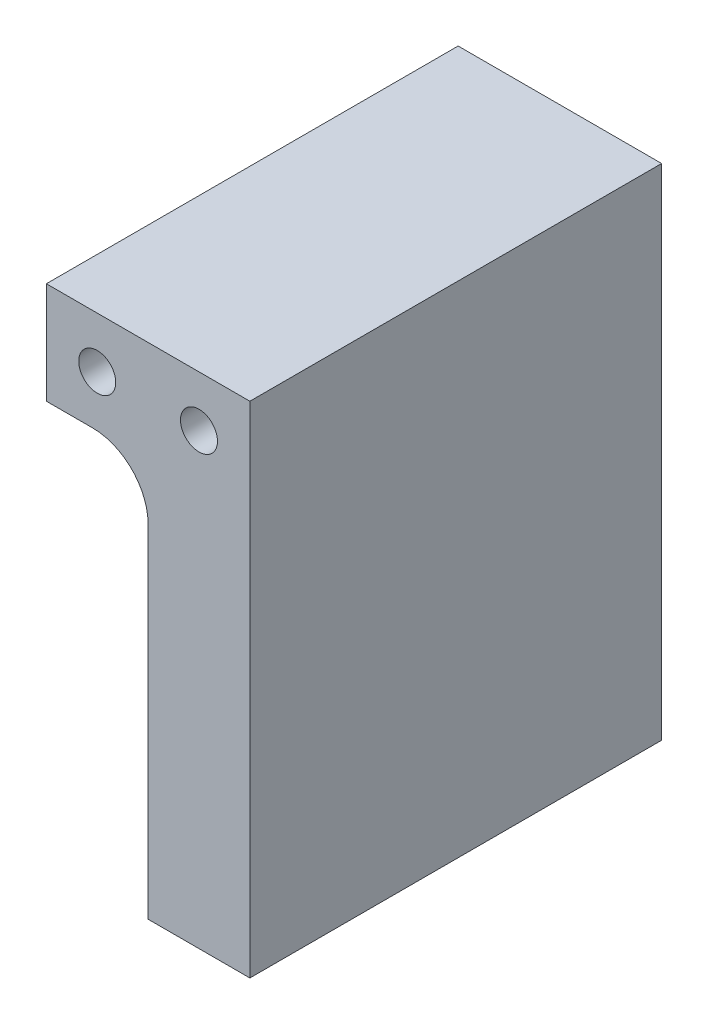
SolidWorks part; units mm, degrees
ref_plane "Front Plane" through (0, 0, 0) normal (0, 0, 1) x (1, 0, 0)
ref_plane "Top Plane" through (0, 0, 0) normal (0, 1, 0) x (1, 0, 0)
ref_plane "Right Plane" through (0, 0, 0) normal (1, 0, 0) x (0, 0, -1)
sketch "Sketch1" plane through (0, 0, 0) normal (0, 0, 1) x (1, 0, 0)
  line L0 (0, 0) -> (-110, 0)
  line L1 (-110, 0) -> (-110, -55)
  line L2 (-110, -55) -> (-85, -55)
  line L3 (-55, -85) -> (-55, -270)
  line L4 (-55, -270) -> (0, -270)
  line L5 (0, -270) -> (0, 0)
  arc A0 (-85, -55) -> (-55, -85) centre (-85, -85) cw
  dimension "D5" = 30
  dimension "D1" = 110
  dimension "D2" = 270
  dimension "D3" = 55
  dimension "D4" = 55
extrude "Boss-Extrude1" add sketch "Sketch1" along normal blind 222.57
sketch "Sketch2" plane through (0, 0, 222.57) normal (0, 0, 1) x (1, 0, 0)
  line L0 (-110, -55) -> (0, -55) construction
  line L1 (0, -270) -> (0, 0) construction
  line L2 (-55, -55) -> (-55, 0) construction
  line L3 (0, 0) -> (-110, 0) construction
  line L4 (-55, -55) -> (-110, 0) construction
  line L5 (-55, -55) -> (0, 0) construction
  point P12 (-82.5, -27.5)
  point P14 (-27.5, -27.5)
  point P15 (-80.5445, 16.7123)
hole_wizard "Ø20.0mm Dowel Hole1" positions "Sketch3" profile "Sketch4" hole size "Ø20.0" standard "ISO" end condition through all
sketch "Sketch3" plane through (0, 0, 222.57) normal (0, 0, 1) x (1, 0, 0)
  point P0 (-82.5, -27.5)
  point P3 (-27.5, -27.5)
sketch "Sketch4" plane through (-82.5, -27.5, 222.57) normal (1, 0, 0) x (0, -1, 0)
  line L0 (0, 0) -> (0, 222.57)
  line L1 (0, 222.57) -> (10, 222.57)
  line L2 (10, 222.57) -> (10, 0)
  line L5 (10, 0) -> (0, 0)
  line L11 (0, -6.35) -> (0, 107.95) construction
  dimension "Thru Hole Dia." = 20
  dimension "Thru Hole Depth" = 222.57
